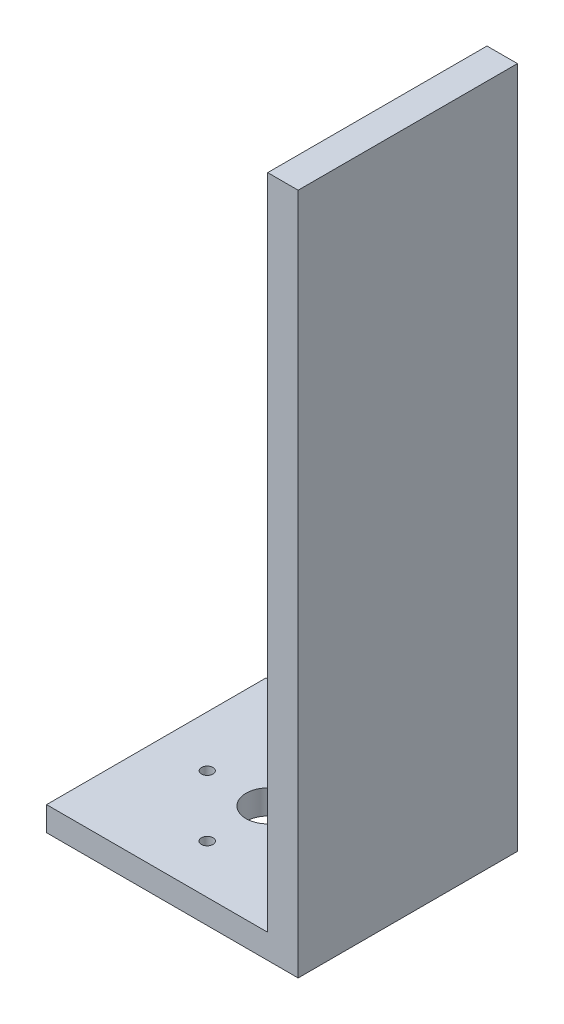
SolidWorks part; units mm, degrees
ref_plane "前视基准面" through (0, 0, 0) normal (0, 0, 1) x (1, 0, 0)
ref_plane "上视基准面" through (0, 0, 0) normal (0, 1, 0) x (1, 0, 0)
ref_plane "右视基准面" through (0, 0, 0) normal (1, 0, 0) x (0, 0, -1)
sketch "草图1" plane through (0, 0, 0) normal (0, 1, 0) x (1, 0, 0)
  line L1 (-200, 45) -> (200, 45)
  line L2 (-200, 45) -> (-200, -45)
  line L3 (-200, -45) -> (200, -45)
  line L4 (200, 45) -> (200, -45)
  line L5 (-200, 45) -> (200, -45) construction
  line L6 (-200, -45) -> (200, 45) construction
  point P0 (0, 0)
  dimension "D1" = 400
  dimension "D2" = 90
extrude "凸台-拉伸1" add sketch "草图1" along normal blind 10
sketch "草图2" plane through (0, 10, 0) normal (0, 1, 0) x (1, 0, 0)
  line L0 (200, -45) -> (200, 45) construction
  circle A0 centre (-6, 0) radius 9.0632
  dimension "D1" = 206
extrude "切除-拉伸1" cut sketch "草图2" against normal blind 10
sketch "草图3" plane through (0, 10, 0) normal (0, 1, 0) x (1, 0, 0)
  circle A0 centre (-6, 0) radius 25 construction
  circle A1 centre (-6, 25) radius 1.8102
  circle A2 centre (19, 0) radius 1.9544
  circle A3 centre (-6, -25) radius 2.3999
  circle A4 centre (-31, 0) radius 2.3599
  dimension "D1" = 50
extrude "切除-拉伸2" cut sketch "草图3" against normal blind 10
sketch "草图4" plane through (0, 10, 0) normal (0, 1, 0) x (1, 0, 0)
  line L0 (-200, 45) -> (-200, -45) construction
  circle A0 centre (-175, -21.5521) radius 6.0734
  circle A1 centre (-135, -21.5521) radius 6.1049
  circle A2 centre (-155, 23.4479) radius 4.7404
  dimension "D1" = 40
  dimension "D2" = 25
  dimension "D3" = 45
  dimension "D4" = 20
extrude "切除-拉伸3" cut sketch "草图4" against normal blind 10
sketch "草图5" plane through (0, 10, 0) normal (0, 1, 0) x (1, 0, 0)
  line L1 (200, 45) -> (-200, 45) construction
  line L2 (38.824, 45) -> (51.3238, 45)
  line L3 (38.824, 45) -> (38.824, -45)
  line L4 (38.824, -45) -> (51.3238, -45)
  line L5 (51.3238, 45) -> (51.3238, -45)
  line L6 (-200, -45) -> (200, -45) construction
extrude "凸台-拉伸2" add sketch "草图5" along normal blind 270
sketch "草图6" plane through (0, 0, 0) normal (0, -1, 0) x (1, 0, 0)
  line L0 (200, -45) -> (-200, -45) construction
  line L1 (-200, 45) -> (-51.9241, 45)
  line L2 (-200, 45) -> (-200, -45)
  line L3 (-200, -45) -> (-51.9241, -45)
  line L4 (-51.9241, 45) -> (-51.9241, -45)
extrude "切除-拉伸4" cut sketch "草图6" against normal blind 10
sketch "草图7" plane through (0, 10, 0) normal (0, 1, 0) x (1, 0, 0)
  line L1 (51.3238, 45) -> (205.0601, 45)
  line L2 (51.3238, 45) -> (51.3238, -61.4292)
  line L3 (51.3238, -61.4292) -> (205.0601, -61.4292)
  line L4 (205.0601, 45) -> (205.0601, -61.4292)
extrude "切除-拉伸5" cut sketch "草图7" against normal blind 10
